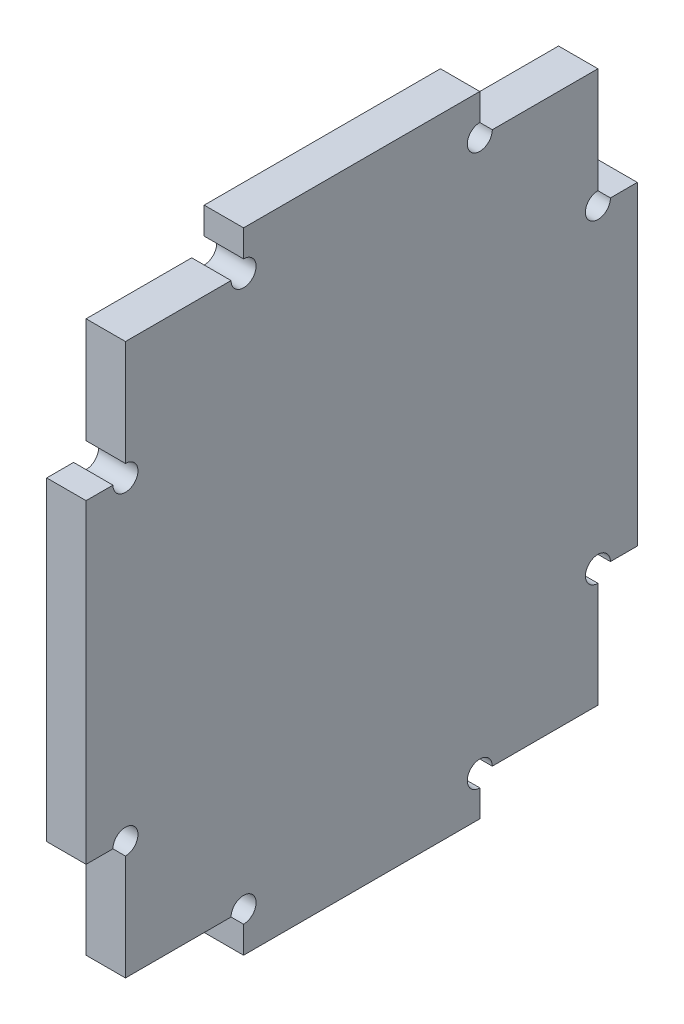
SolidWorks part; units mm, degrees
material "Acrylic (Medium-high impact)"
ref_plane "Front Plane" through (0, 0, 0) normal (0, 0, 1) x (1, 0, 0)
ref_plane "Top Plane" through (0, 0, 0) normal (0, 1, 0) x (1, 0, 0)
ref_plane "Right Plane" through (0, 0, 0) normal (1, 0, 0) x (0, 0, -1)
sketch "Sketch1" plane through (0, 0, 0) normal (1, 0, 0) x (0, 0, -1)
  line L1 (-35, -40) -> (35, -40)
  line L2 (-35, -40) -> (-35, 40)
  line L3 (-35, 40) -> (35, 40)
  line L4 (35, -40) -> (35, 40)
  line L5 (-35, -40) -> (35, 40) construction
  line L6 (-35, 40) -> (35, -40) construction
  point P0 (0, 0)
  dimension "D1" = 70
  dimension "D2" = 80
extrude "Boss-Extrude1" add sketch "Sketch1" along normal blind 5
sketch "Sketch3" plane through (5, 0, 0) normal (1, 0, 0) x (0, 0, -1)
  line L0 (-35, 20) -> (-30, 20)
  line L1 (-35, 40) -> (-35, -40) construction
  line L2 (-30, 20) -> (-30, 35)
  line L3 (-30, 35) -> (-15, 35)
  line L4 (-15, 35) -> (-15, 40)
  line L5 (35, 40) -> (-35, 40) construction
  line L6 (-15, 40) -> (-35, 40)
  line L7 (-35, 40) -> (-35, 20)
  dimension "D1" = 20
  dimension "D2" = 5
extrude "Cut-Extrude1" cut sketch "Sketch3" against normal through all both and the other way through all
mirror "Mirror1" about plane through (0, 0, 0) normal (0, 0, 1) of "Cut-Extrude1" second plane through (0, 0, 0) second plane normal (0, 1, 0)
sketch "Sketch4" plane through (5, 0, 0) normal (1, 0, 0) x (0, 0, -1)
  circle A0 centre (-30, 20) radius 1.5875
  circle A1 centre (-15, 35) radius 1.5875
  circle A2 centre (15, 35) radius 1.5875
  circle A3 centre (30, 20) radius 1.5875
  circle A4 centre (30, -20) radius 1.5875
  circle A5 centre (15, -35) radius 1.5875
  circle A6 centre (-15, -35) radius 1.5875
  circle A7 centre (-30, -20) radius 1.5875
  point P26 (0, 0)
  dimension "D1" = 3.175
extrude "Cut-Extrude2" cut sketch "Sketch4" against normal through all
